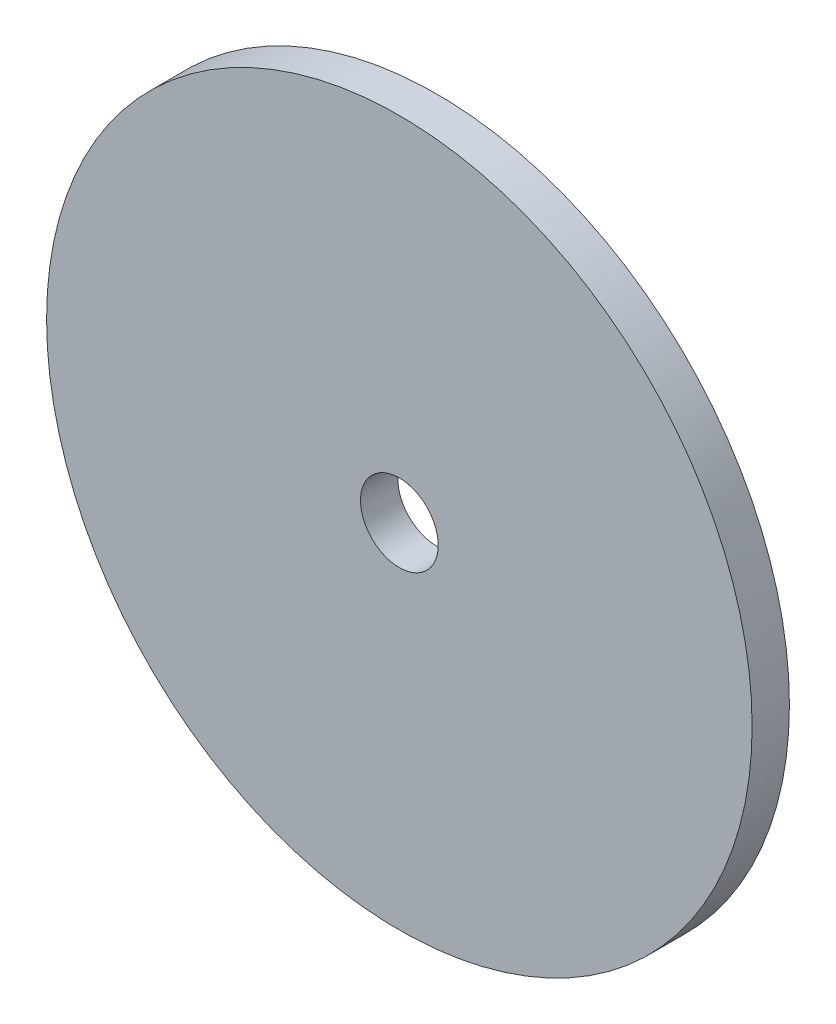
SolidWorks part; units mm, degrees
ref_plane "Front Plane" through (0, 0, 0) normal (0, 0, 1) x (1, 0, 0)
ref_plane "Top Plane" through (0, 0, 0) normal (0, 1, 0) x (1, 0, 0)
ref_plane "Right Plane" through (0, 0, 0) normal (1, 0, 0) x (0, 0, -1)
sketch "Sketch1" plane through (0, 0, 0) normal (0, 0, 1) x (1, 0, 0)
  circle A0 centre (0, 0) radius 28.829
  dimension "D1" = 57.658
extrude "Boss-Extrude1" add sketch "Sketch1" along normal blind 3.048
sketch "Sketch2" plane through (0, 0, 3.048) normal (0, 0, 1) x (1, 0, 0)
  circle A0 centre (0, 0) radius 3.175
  dimension "D1" = 6.35
extrude "Cut-Extrude1" cut sketch "Sketch2" against normal blind 3.048
